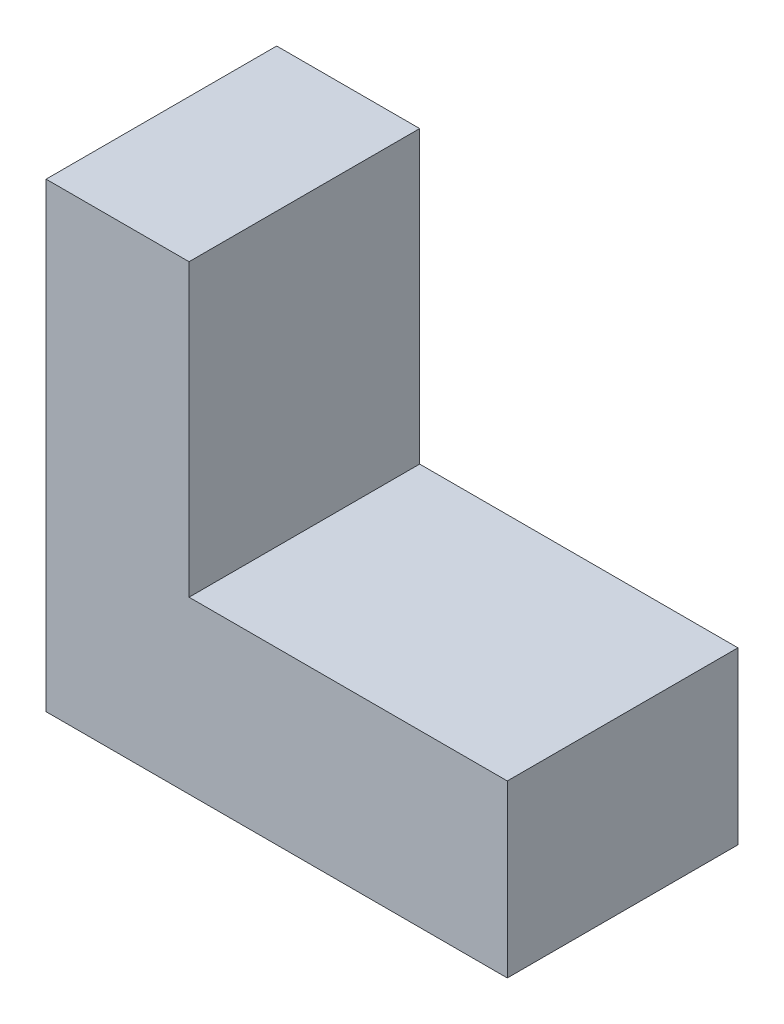
SolidWorks part; units mm, degrees
material "1060 Alloy"
ref_plane "Front Plane" through (0, 0, 0) normal (0, 0, 1) x (1, 0, 0)
ref_plane "Top Plane" through (0, 0, 0) normal (0, 1, 0) x (1, 0, 0)
ref_plane "Right Plane" through (0, 0, 0) normal (1, 0, 0) x (0, 0, -1)
sketch "Sketch1" plane through (0, 0, 0) normal (0, 0, 1) x (1, 0, 0)
  line L1 (0, 0) -> (50, 0)
  line L2 (0, 0) -> (0, 18.5)
  line L3 (0, 18.5) -> (50, 18.5)
  line L4 (50, 0) -> (50, 18.5)
  dimension "D1" = 18.5
  dimension "D2" = 50
extrude "Boss-Extrude1" add sketch "Sketch1" along normal blind 25
sketch "Sketch2" plane through (0, 0, 0) normal (0, -1, 0) x (1, 0, 0)
  line L0 (0, 25) -> (50, 25) construction
  line L1 (0, 0) -> (15.5, 0)
  line L2 (0, 0) -> (0, 25)
  line L3 (0, 25) -> (15.5, 25)
  line L4 (15.5, 0) -> (15.5, 25)
  dimension "D1" = 15.5
extrude "Boss-Extrude2" add sketch "Sketch2" against normal blind 50
sketch "Sketch4" plane through (0, 0, 0) normal (0, 0, -1) x (-1, 0, 0)
  line L0 (0, 50) -> (-15.5, 50) construction
  line L1 (0, 50) -> (0, 0) construction
  circle A0 centre (-5, 45) radius 2.612 construction
  dimension "D1" = 5
  dimension "D2" = 5
